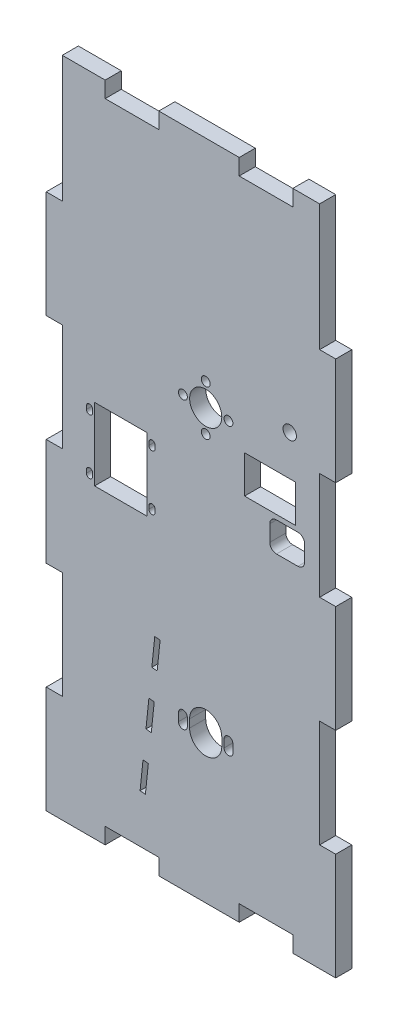
SolidWorks part; units mm, degrees
ref_plane "Face" through (0, 0, 0) normal (0, 0, 1) x (1, 0, 0)
ref_plane "Dessus" through (0, 0, 0) normal (0, 1, 0) x (1, 0, 0)
ref_plane "Droite" through (0, 0, 0) normal (1, 0, 0) x (0, 0, -1)
sketch "Esquisse1" plane through (0, 0, -2) normal (0, 0, 1) x (1, 0, 0)
  line L0 (2351.7238, 171.4099) -> (2351.7238, -55.6932) construction
  line L1 (2459.7238, -65.6932) -> (2443.7238, -65.6932)
  line L2 (2459.7238, -65.6932) -> (2459.7238, -25.6932)
  line L4 (2351.7238, -65.6932) -> (2351.7238, -25.6932)
  line L5 (2451.7238, -65.6932) -> (2361.7238, -65.6932) construction
  line L8 (2369.7738, 75.3068) -> (2369.7738, 48.3068) construction
  line L9 (2366.7238, 71.5068) -> (2366.7238, 72.7068) construction
  line L10 (2369.0238, 72.7068) -> (2369.0238, 71.5068) construction
  line L11 (2392.3238, 72.7068) -> (2392.3238, 71.5068) construction
  line L12 (2390.0238, 71.5068) -> (2390.0238, 72.7068) construction
  line L13 (2389.2738, 75.3068) -> (2369.7738, 75.3068) construction
  line L14 (2389.2738, 48.3068) -> (2389.2738, 75.3068) construction
  line L15 (2392.3238, 52.1068) -> (2392.3238, 50.9068) construction
  line L16 (2390.0238, 50.9068) -> (2390.0238, 52.1068) construction
  line L17 (2366.7238, 52.1068) -> (2366.7238, 50.9068) construction
  line L18 (2369.0238, 50.9068) -> (2369.0238, 52.1068) construction
  line L19 (2369.7738, 48.3068) -> (2389.2738, 48.3068) construction
  line L24 (2459.7238, -25.6932) -> (2459.7238, -65.6932) construction
  line L27 (2357.7238, 181.4099) -> (2373.7238, 181.4099)
  line L28 (2418.0738, -9.1932) -> (2418.0738, -12.1932) construction
  line L29 (2421.3738, -12.1932) -> (2421.3738, -9.1932) construction
  line L30 (2401.0738, -9.1932) -> (2401.0738, -12.1932) construction
  line L31 (2404.3738, -12.1932) -> (2404.3738, -9.1932) construction
  line L32 (2405.2238, -9.1932) -> (2405.2238, -12.1932) construction
  line L33 (2417.2238, -12.1932) -> (2417.2238, -9.1932) construction
  line L34 (2369.7738, 75.3068) -> (2369.7738, 48.3068)
  line L35 (2366.7238, 71.5068) -> (2366.7238, 72.7068)
  line L36 (2369.0238, 72.7068) -> (2369.0238, 71.5068)
  line L37 (2392.3238, 72.7068) -> (2392.3238, 71.5068)
  line L38 (2390.0238, 71.5068) -> (2390.0238, 72.7068)
  line L39 (2389.2738, 75.3068) -> (2369.7738, 75.3068)
  line L40 (2389.2738, 48.3068) -> (2389.2738, 75.3068)
  line L41 (2392.3238, 52.1068) -> (2392.3238, 50.9068)
  line L42 (2390.0238, 50.9068) -> (2390.0238, 52.1068)
  line L43 (2366.7238, 52.1068) -> (2366.7238, 50.9068)
  line L44 (2369.0238, 50.9068) -> (2369.0238, 52.1068)
  line L45 (2369.7738, 48.3068) -> (2389.2738, 48.3068)
  line L54 (2418.0738, -9.1932) -> (2418.0738, -12.1932)
  line L55 (2421.3738, -12.1932) -> (2421.3738, -9.1932)
  line L56 (2401.0738, -9.1932) -> (2401.0738, -12.1932)
  line L57 (2404.3738, -12.1932) -> (2404.3738, -9.1932)
  line L58 (2405.2238, -9.1932) -> (2405.2238, -12.1932)
  line L59 (2417.2238, -12.1932) -> (2417.2238, -9.1932)
  line L60 (2459.7238, -25.6932) -> (2453.7238, -25.6932)
  line L61 (2459.7238, 14.3068) -> (2459.7238, 54.3068)
  line L62 (2453.7238, -25.6932) -> (2453.7238, 14.3068)
  line L63 (2453.7238, 14.3068) -> (2459.7238, 14.3068)
  line L64 (2459.7238, 54.3068) -> (2453.7238, 54.3068)
  line L65 (2453.7238, 54.3068) -> (2453.7238, 94.3068)
  line L66 (2453.7238, 94.3068) -> (2459.7238, 94.3068)
  line L67 (2459.7238, 134.3068) -> (2453.7238, 134.3068)
  line L68 (2453.7238, 134.3068) -> (2453.7238, 181.4099)
  line L70 (2459.7238, 94.3068) -> (2459.7238, 134.3068)
  line L74 (2459.7238, 134.3068) -> (2459.7238, 181.4105) construction
  line L75 (2443.7238, 74.0108) -> (2426.7238, 74.0108) construction
  line L84 (2426.7238, 74.0108) -> (2426.7238, 86.0108) construction
  line L85 (2426.7238, 86.0108) -> (2443.7238, 86.0108) construction
  line L86 (2443.7238, 74.0108) -> (2443.7238, 86.0108) construction
  line L87 (2443.7238, 74.0108) -> (2426.7238, 74.0108) construction
  line L88 (2426.7238, 74.0108) -> (2426.7238, 86.0108) construction
  line L89 (2426.7238, 86.0108) -> (2443.7238, 86.0108) construction
  line L90 (2443.7238, 74.0108) -> (2443.7238, 86.0108) construction
  line L91 (2444.7238, 73.0108) -> (2425.7238, 73.0108)
  line L92 (2425.7238, 73.0108) -> (2425.7238, 87.0108)
  line L93 (2425.7238, 87.0108) -> (2444.7238, 87.0108)
  line L94 (2444.7238, 73.0108) -> (2444.7238, 87.0108)
  line L127 (2445.6238, 61.2568) -> (2437.6238, 61.2568) construction
  line L128 (2436.1238, 62.7568) -> (2436.1238, 68.7568) construction
  line L129 (2437.6238, 70.2568) -> (2445.6238, 70.2568) construction
  line L130 (2447.1238, 68.7568) -> (2447.1238, 62.7568) construction
  line L131 (2393.7238, -59.6932) -> (2393.7238, -65.6932)
  line L132 (2445.6238, 61.2568) -> (2437.6238, 61.2568) construction
  line L133 (2373.7238, -59.6932) -> (2393.7238, -59.6932)
  line L134 (2373.7238, -59.6932) -> (2373.7238, -65.6932)
  line L135 (2443.7238, -59.6932) -> (2443.7238, -65.6932)
  line L137 (2423.7238, -59.6932) -> (2443.7238, -59.6932)
  line L138 (2423.7238, -59.6932) -> (2423.7238, -65.6932)
  line L139 (2423.7238, -65.6932) -> (2393.7238, -65.6932)
  line L140 (2436.1238, 62.7568) -> (2436.1238, 68.7568) construction
  line L141 (2437.6238, 70.2568) -> (2445.6238, 70.2568) construction
  line L142 (2447.1238, 68.7568) -> (2447.1238, 62.7568) construction
  line L143 (2448.1238, 68.7568) -> (2448.1238, 62.7568)
  line L144 (2445.6238, 60.2568) -> (2437.6238, 60.2568)
  line L145 (2435.1238, 62.7568) -> (2435.1238, 68.7568)
  line L146 (2437.6238, 71.2568) -> (2445.6238, 71.2568)
  line L155 (2459.7238, 181.4099) -> (2453.7238, 181.4099) construction
  line L187 (2373.7238, -65.6932) -> (2351.7238, -65.6932)
  line L192 (2386.7391, -41.665) -> (2387.836, -31.1506) construction
  line L193 (2387.836, -31.1506) -> (2389.8252, -31.3582) construction
  line L194 (2389.8252, -31.3582) -> (2388.7283, -41.8725) construction
  line L195 (2388.7283, -41.8725) -> (2386.7391, -41.665) construction
  line L196 (2388.933, -20.6363) -> (2390.0299, -10.1219) construction
  line L197 (2390.0299, -10.1219) -> (2392.0191, -10.3294) construction
  line L198 (2392.0191, -10.3294) -> (2390.9222, -20.8438) construction
  line L199 (2390.9222, -20.8438) -> (2388.933, -20.6363) construction
  line L200 (2391.1269, 0.3924) -> (2392.2238, 10.9068) construction
  line L201 (2392.2238, 10.9068) -> (2394.213, 10.6993) construction
  line L202 (2394.213, 10.6993) -> (2393.1161, 0.1849) construction
  line L203 (2393.1161, 0.1849) -> (2391.1269, 0.3924) construction
  line L208 (2386.7391, -41.665) -> (2387.836, -31.1506)
  line L209 (2387.836, -31.1506) -> (2389.8252, -31.3582)
  line L210 (2389.8252, -31.3582) -> (2388.7283, -41.8725)
  line L211 (2388.7283, -41.8725) -> (2386.7391, -41.665)
  line L212 (2388.933, -20.6363) -> (2390.0299, -10.1219)
  line L213 (2390.0299, -10.1219) -> (2392.0191, -10.3294)
  line L214 (2392.0191, -10.3294) -> (2390.9222, -20.8438)
  line L215 (2390.9222, -20.8438) -> (2388.933, -20.6363)
  line L216 (2391.1269, 0.3924) -> (2392.2238, 10.9068)
  line L217 (2392.2238, 10.9068) -> (2394.213, 10.6993)
  line L218 (2394.213, 10.6993) -> (2393.1161, 0.1849)
  line L219 (2393.1161, 0.1849) -> (2391.1269, 0.3924)
  line L220 (2453.7238, 181.4099) -> (2453.7238, 174.308) construction
  line L221 (2474.7238, 181.4105) -> (2459.7238, 181.4105) construction
  line L222 (2393.7238, 181.4099) -> (2393.7238, 175.4099)
  line L224 (2443.7238, 181.4099) -> (2443.7238, 175.4099)
  line L225 (2443.7238, 175.4099) -> (2423.7238, 175.4099)
  line L226 (2423.7238, 181.4099) -> (2423.7238, 175.4099)
  line L228 (2373.7238, 181.4099) -> (2373.7238, 175.4099)
  line L229 (2393.7238, 175.4099) -> (2373.7238, 175.4099)
  line L230 (2443.7238, 181.4099) -> (2453.7238, 181.4099)
  line L231 (2393.7238, 181.4099) -> (2423.7238, 181.4099)
  line L232 (2405.7238, -130.9998) -> (2405.7238, 241.5411) construction
  line L233 (2351.7238, -25.6932) -> (2357.7238, -25.6932)
  line L235 (2357.7238, 14.3068) -> (2351.7238, 14.3068)
  line L237 (2351.7238, 54.3068) -> (2357.7238, 54.3068)
  line L238 (2357.7238, 94.3068) -> (2351.7238, 94.3068)
  line L239 (2351.7238, 134.3068) -> (2357.7238, 134.3068)
  line L241 (2357.7238, -25.6932) -> (2357.7238, 14.3068)
  line L242 (2357.7238, 54.3068) -> (2357.7238, 94.3068)
  line L243 (2357.7238, 134.3068) -> (2357.7238, 181.4099)
  line L244 (2351.7238, 94.3068) -> (2351.7238, 134.3068)
  line L245 (2351.7238, 14.3068) -> (2351.7238, 54.3068)
  line L246 (2383.8656, -59.6932) -> (2393.7238, -59.6932) [skipped]
  circle A0 centre (2411.2238, 102.8068) radius 1.65 construction
  circle A1 centre (2419.7238, 94.3069) radius 1.65 construction
  circle A2 centre (2411.2238, 94.3068) radius 6 construction
  circle A3 centre (2402.7238, 94.3068) radius 1.65 construction
  circle A4 centre (2411.2238, 85.8068) radius 1.65 construction
  arc A5 (2369.0238, 72.7068) -> (2366.7238, 72.7068) centre (2367.8738, 72.7068) ccw construction
  arc A6 (2366.7238, 71.5068) -> (2369.0238, 71.5068) centre (2367.8738, 71.5068) ccw construction
  arc A7 (2390.0238, 71.5068) -> (2392.3238, 71.5068) centre (2391.1738, 71.5068) ccw construction
  arc A8 (2392.3238, 72.7068) -> (2390.0238, 72.7068) centre (2391.1738, 72.7068) ccw construction
  arc A9 (2392.3238, 52.1068) -> (2390.0238, 52.1068) centre (2391.1738, 52.1068) ccw construction
  arc A10 (2390.0238, 50.9068) -> (2392.3238, 50.9068) centre (2391.1738, 50.9068) ccw construction
  arc A11 (2369.0238, 52.1068) -> (2366.7238, 52.1068) centre (2367.8738, 52.1068) ccw construction
  arc A12 (2366.7238, 50.9068) -> (2369.0238, 50.9068) centre (2367.8738, 50.9068) ccw construction
  arc A18 (2418.0738, -12.1932) -> (2421.3738, -12.1932) centre (2419.7238, -12.1932) ccw construction
  arc A19 (2421.3738, -9.1932) -> (2418.0738, -9.1932) centre (2419.7238, -9.1932) ccw construction
  arc A20 (2404.3738, -9.1932) -> (2401.0738, -9.1932) centre (2402.7238, -9.1932) ccw construction
  arc A21 (2401.0738, -12.1932) -> (2404.3738, -12.1932) centre (2402.7238, -12.1932) ccw construction
  arc A22 (2417.2238, -9.1932) -> (2405.2238, -9.1932) centre (2411.2238, -9.1932) ccw construction
  arc A23 (2405.2238, -12.1932) -> (2417.2238, -12.1932) centre (2411.2238, -12.1932) ccw construction
  circle A24 centre (2411.2238, 102.8068) radius 1.65
  circle A25 centre (2419.7238, 94.3069) radius 1.65
  circle A26 centre (2411.2238, 94.3068) radius 6
  circle A27 centre (2402.7238, 94.3068) radius 1.65
  circle A28 centre (2411.2238, 85.8068) radius 1.65
  arc A29 (2369.0238, 72.7068) -> (2366.7238, 72.7068) centre (2367.8738, 72.7068) ccw
  arc A30 (2366.7238, 71.5068) -> (2369.0238, 71.5068) centre (2367.8738, 71.5068) ccw
  arc A31 (2390.0238, 71.5068) -> (2392.3238, 71.5068) centre (2391.1738, 71.5068) ccw
  arc A32 (2392.3238, 72.7068) -> (2390.0238, 72.7068) centre (2391.1738, 72.7068) ccw
  arc A33 (2392.3238, 52.1068) -> (2390.0238, 52.1068) centre (2391.1738, 52.1068) ccw
  arc A34 (2390.0238, 50.9068) -> (2392.3238, 50.9068) centre (2391.1738, 50.9068) ccw
  arc A35 (2369.0238, 52.1068) -> (2366.7238, 52.1068) centre (2367.8738, 52.1068) ccw
  arc A36 (2366.7238, 50.9068) -> (2369.0238, 50.9068) centre (2367.8738, 50.9068) ccw
  arc A42 (2418.0738, -12.1932) -> (2421.3738, -12.1932) centre (2419.7238, -12.1932) ccw
  arc A43 (2421.3738, -9.1932) -> (2418.0738, -9.1932) centre (2419.7238, -9.1932) ccw
  arc A44 (2404.3738, -9.1932) -> (2401.0738, -9.1932) centre (2402.7238, -9.1932) ccw
  arc A45 (2401.0738, -12.1932) -> (2404.3738, -12.1932) centre (2402.7238, -12.1932) ccw
  arc A46 (2417.2238, -9.1932) -> (2405.2238, -9.1932) centre (2411.2238, -9.1932) ccw
  arc A47 (2405.2238, -12.1932) -> (2417.2238, -12.1932) centre (2411.2238, -12.1932) ccw
  arc A48 (2445.6238, 61.2568) -> (2447.1238, 62.7568) centre (2445.6238, 62.7568) ccw construction
  arc A49 (2436.1238, 62.7568) -> (2437.6238, 61.2568) centre (2437.6238, 62.7568) ccw construction
  arc A50 (2437.6238, 70.2568) -> (2436.1238, 68.7568) centre (2437.6238, 68.7568) ccw construction
  arc A51 (2447.1238, 68.7568) -> (2445.6238, 70.2568) centre (2445.6238, 68.7568) ccw construction
  arc A52 (2445.6238, 61.2568) -> (2447.1238, 62.7568) centre (2445.6238, 62.7568) ccw construction
  arc A53 (2436.1238, 62.7568) -> (2437.6238, 61.2568) centre (2437.6238, 62.7568) ccw construction
  arc A54 (2437.6238, 70.2568) -> (2436.1238, 68.7568) centre (2437.6238, 68.7568) ccw construction
  arc A55 (2447.1238, 68.7568) -> (2445.6238, 70.2568) centre (2445.6238, 68.7568) ccw construction
  arc A56 (2445.6238, 60.2568) -> (2448.1238, 62.7568) centre (2445.6238, 62.7568) ccw
  arc A57 (2435.1238, 62.7568) -> (2437.6238, 60.2568) centre (2437.6238, 62.7568) ccw
  arc A58 (2437.6238, 71.2568) -> (2435.1238, 68.7568) centre (2437.6238, 68.7568) ccw
  arc A59 (2448.1238, 68.7568) -> (2445.6238, 71.2568) centre (2445.6238, 68.7568) ccw
  circle A60 centre (2442.5738, 102.0108) radius 2.5 construction
  circle A61 centre (2442.5738, 102.0108) radius 2.5
  point P3 (0, 0)
  point P10 (0, 0)
  point P78 (0, 0)
  dimension "D1" = 40
  dimension "D2" = 40
  dimension "D3" = 6
  dimension "D5" = 40
  dimension "D6" = 20
  dimension "D8" = 16
  dimension "D9" = 6
  dimension "D10" = 2
  dimension "D11" = 30
  dimension "D12" = 2
  dimension "D4" = 1
  dimension "D7" = 1
extrude "Boss.-Extru.1" add sketch "Esquisse1" along normal blind 6
